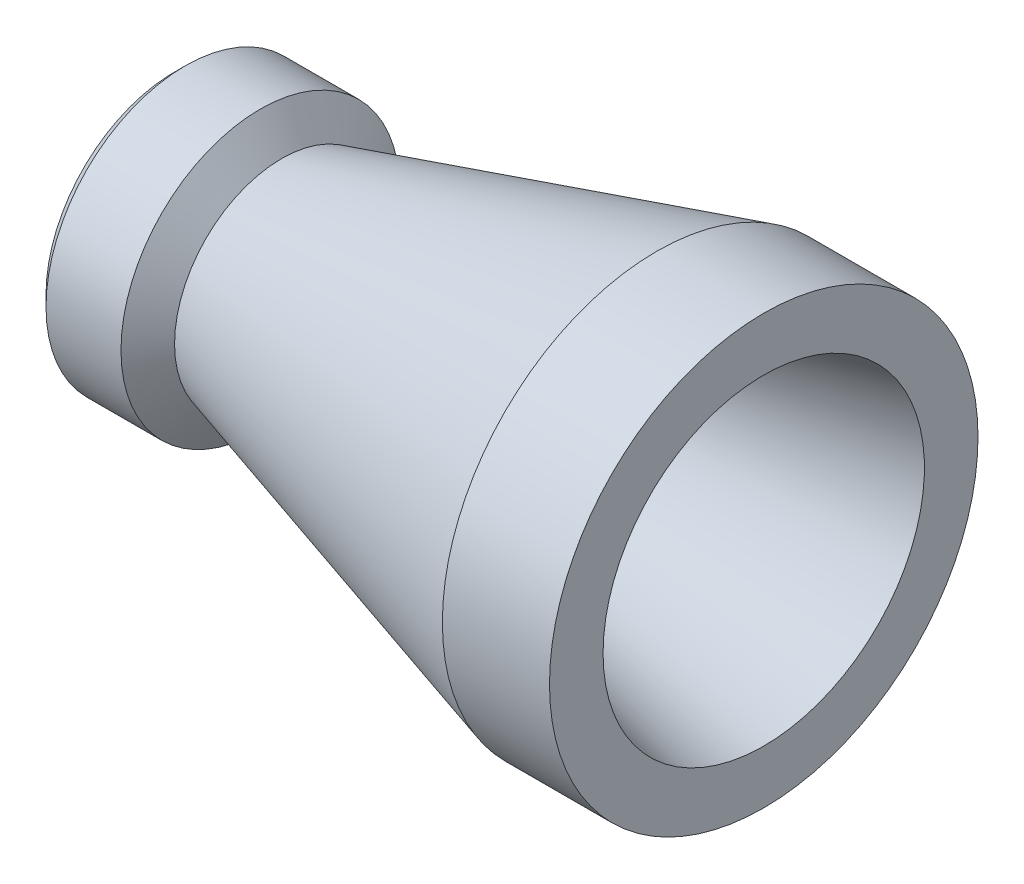
SolidWorks part; units mm, degrees
ref_plane "前基準面" through (0, 0, 0) normal (0, 0, 1) x (1, 0, 0)
ref_plane "上基準面" through (0, 0, 0) normal (0, 1, 0) x (1, 0, 0)
ref_plane "右基準面" through (0, 0, 0) normal (1, 0, 0) x (0, 0, -1)
sketch "草圖1" plane through (0, 0, 0) normal (0, 0, 1) x (1, 0, 0)
  line L0 (0, 0) -> (65.2536, 0) construction
  line L1 (0, 5) -> (0, 12)
  line L2 (1, 13) -> (8, 13)
  line L3 (8, 13) -> (10, 10)
  line L4 (10, 10) -> (45, 20)
  line L5 (45, 20) -> (55, 20)
  line L6 (55, 20) -> (55, 15)
  line L7 (55, 15) -> (23.5568, 7.8538)
  line L8 (22, 5.9035) -> (22, 5)
  line L9 (22, 5) -> (0, 5)
  line L10 (0, 0) -> (0, 26.747) construction
  line L11 (0, 12) -> (1, 13)
  arc A0 (22, 5.9035) -> (23.5568, 7.8538) centre (24, 5.9035) cw
  point P5 (0, 13)
  point P15 (22, 7.5)
  point P18 (0, 0)
  dimension "D7" = 2
  dimension "D1" = 20
  dimension "D2" = 10
  dimension "D3" = 2
  dimension "D4" = 10
  dimension "D5" = 30
  dimension "D6" = 15
  dimension "D8" = 10
  dimension "D9" = 22
  dimension "D10" = 55
  dimension "D11" = 40
  dimension "D12" = 26
revolve "旋轉1" add sketch "草圖1" angle 360 about L0
